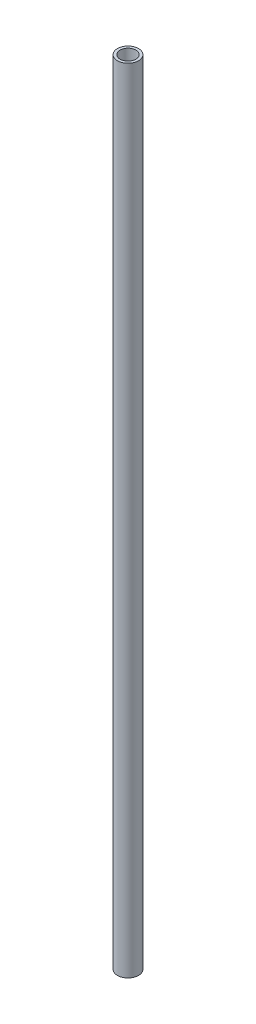
SolidWorks part; units mm, degrees
ref_plane "Спереди" through (0, 0, 0) normal (0, 0, 1) x (1, 0, 0)
ref_plane "Сверху" through (0, 0, 0) normal (0, 1, 0) x (1, 0, 0)
ref_plane "Справа" through (0, 0, 0) normal (1, 0, 0) x (0, 0, -1)
sketch "Эскиз1" plane through (0, 0, 0) normal (0, 1, 0) x (1, 0, 0)
  circle A0 centre (0, 0) radius 4
  circle A1 centre (0, 0) radius 3
  dimension "D1" = 8
  dimension "D2" = 6
extrude "Бобышка-Вытянуть1" add sketch "Эскиз1" along normal blind 300
